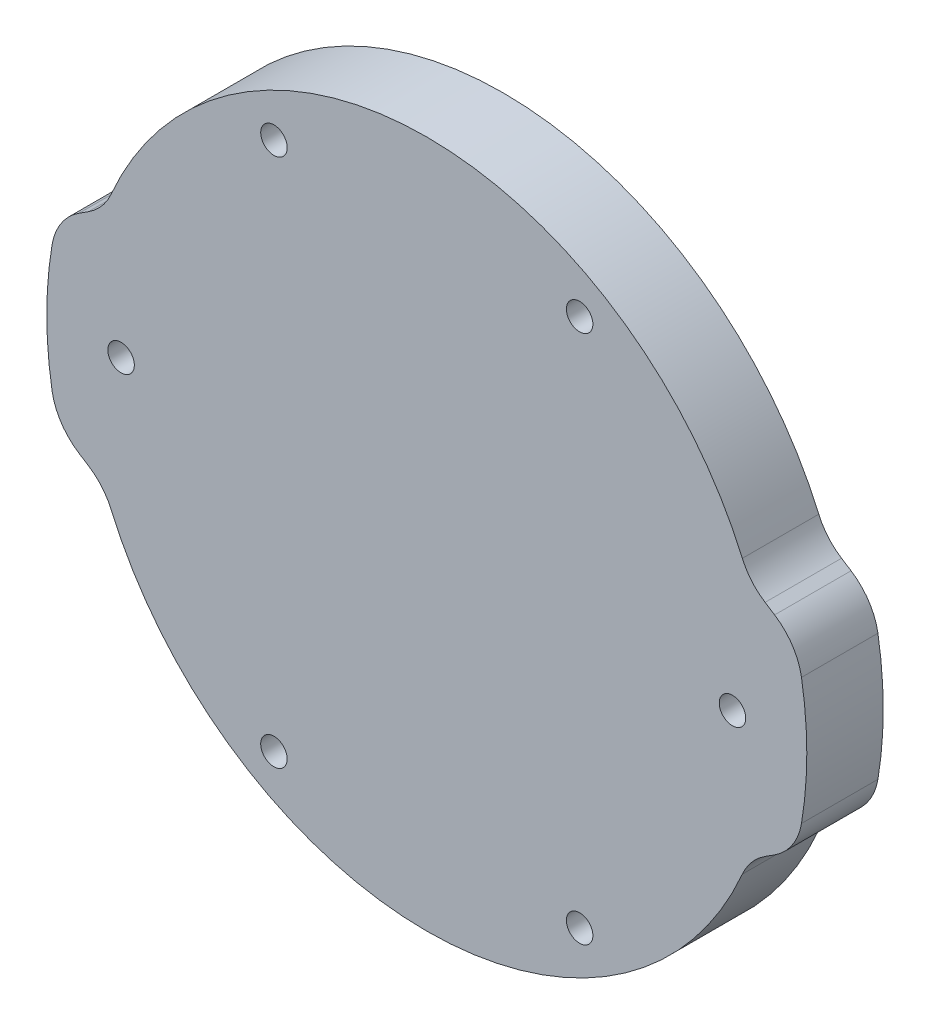
SolidWorks part; units mm, degrees
material "ABS PC"
ref_plane "Front Plane" through (0, 0, 0) normal (0, 0, 1) x (1, 0, 0)
ref_plane "Top Plane" through (0, 0, 0) normal (0, 1, 0) x (1, 0, 0)
ref_plane "Right Plane" through (0, 0, 0) normal (1, 0, 0) x (0, 0, -1)
sketch "Sketch1" plane through (0, 0, 0) normal (0, 0, 1) x (1, 0, 0)
  line L0 (-30.6713, 7.5) -> (-26.7681, 10)
  line L1 (-30.6713, -7.5) -> (-26.7681, -10)
  line L2 (30.6713, 7.5) -> (26.7681, 10)
  line L3 (30.6713, -7.5) -> (26.7681, -10)
  line L4 (0, 0) -> (-12.7, 21.997) construction
  line L5 (-12.7, 21.997) -> (-14.2875, 24.7467) construction
  line L6 (-25.4, 0) -> (0, 0) construction
  arc A0 (-26.7681, -10) -> (26.7681, -10) centre (0, 0) ccw
  circle A1 centre (-25.4, 0) radius 1.1
  circle A2 centre (-12.7, 21.997) radius 1.1
  circle A3 centre (12.7, 21.997) radius 1.1
  circle A4 centre (25.4, 0) radius 1.1
  circle A5 centre (12.7, -21.997) radius 1.1
  circle A6 centre (-12.7, -21.997) radius 1.1
  arc A7 (-30.6713, 7.5) -> (-30.6713, -7.5) centre (0, 0) ccw
  arc A8 (30.6713, 7.5) -> (30.6713, -7.5) centre (0, 0) cw
  arc A9 (26.7681, 10) -> (-26.7681, 10) centre (0, 0) ccw
  point P17 (0, 0)
  point P19 (-31.575, 0)
  point P24 (31.575, 0)
  dimension "D1" = 57.15
  dimension "D3" = 2.2
  dimension "D6" = 3
  dimension "D8" = 3
  dimension "D5" = 20
  dimension "D7" = 15
  dimension "D9" = 3.175
  dimension "D4" = 6
extrude "Boss-Extrude1" add sketch "Sketch1" along normal blind 6.35
fillet "Fillet1" radius 5 8 edges at (26.7681, 10, 3.175) (30.6713, 7.5, 3.175) (30.6713, -7.5, 3.175) (26.7681, -10, 3.175) (-26.7681, -10, 3.175) (-30.6713, -7.5, 3.175) (-26.7681, 10, 3.175) (-30.6713, 7.5, 3.175)
sketch "Sketch2" plane through (0, 0, 0) normal (0, 0, 1) x (1, 0, 0)
  circle A0 centre (0, 0) radius 19 construction
  dimension "D1" = 38
